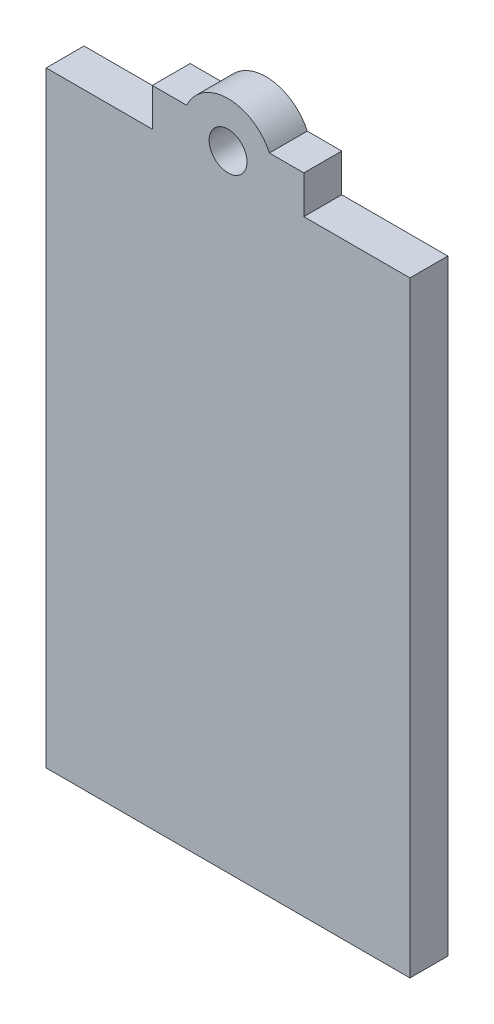
SolidWorks part; units mm, degrees
ref_plane "Front Plane" through (0, 0, 0) normal (0, 0, 1) x (1, 0, 0)
ref_plane "Top Plane" through (0, 0, 0) normal (0, 1, 0) x (1, 0, 0)
ref_plane "Right Plane" through (0, 0, 0) normal (1, 0, 0) x (0, 0, -1)
sketch "Sketch1" plane through (0, 0, 0) normal (0, 0, 1) x (1, 0, 0)
  line L1 (24, 50) -> (-24, 50)
  line L2 (24, 50) -> (24, -50)
  line L3 (24, -50) -> (-24, -50)
  line L4 (-24, 50) -> (-24, -50)
  line L5 (24, 50) -> (-24, -50) construction
  line L6 (24, -50) -> (-24, 50) construction
  point P0 (0, 0)
  dimension "D1" = 48
  dimension "D2" = 100
extrude "Boss-Extrude1" add sketch "Sketch1" along normal blind 5
sketch "Sketch2" plane through (0, 50, 0) normal (0, 1, 0) x (1, 0, 0)
  line L0 (24, -5) -> (-24, -5) construction
  line L1 (-10, -5) -> (10, -5)
  line L2 (-10, -5) -> (-10, 0)
  line L3 (-10, 0) -> (10, 0)
  line L4 (10, -5) -> (10, 0)
  line L5 (24, 0) -> (-24, 0) construction
  line L6 (-24, -5) -> (-24, 0) construction
  line L8 (24, -5) -> (24, 0) construction
  dimension "D1" = 14
  dimension "D2" = 20
  dimension "D3" = 14
  dimension "D4" = 5
extrude "Boss-Extrude2" add sketch "Sketch2" along normal blind 5
mirror "Mirror1" about plane through (0, 0, 0) normal (0, 1, 0) of "Boss-Extrude2"
sketch "Sketch3" plane through (0, 0, 5) normal (0, 0, 1) x (1, 0, 0)
  line L0 (-10, 55) -> (10, 55) construction
  line L1 (-10, 50) -> (-24, 50) construction
  line L2 (10, 55) -> (10, 50) construction
  line L3 (-10, 55) -> (-10, 50) construction
  circle A0 centre (0, 52.5) radius 6
  dimension "D1" = 12
  dimension "D2" = 2.5
  dimension "D3" = 10
  dimension "D4" = 2.5
  dimension "D5" = 10
extrude "Boss-Extrude3" add sketch "Sketch3" against normal blind 5
sketch "Sketch4" plane through (0, 0, 5) normal (0, 0, 1) x (1, 0, 0)
  line L0 (10, 55) -> (10, 50) construction
  line L1 (5.4544, 55) -> (10, 55) construction
  line L2 (-10, 55) -> (-5.4544, 55) construction
  circle A0 centre (0, 52.5) radius 2.5
  arc A2 (5.4544, 55) -> (-5.4544, 55) centre (0, 52.5) ccw construction
  dimension "D1" = 5
  dimension "D2" = 10
  dimension "D3" = 2.5
  dimension "D4" = 3.5
extrude "Cut-Extrude1" cut sketch "Sketch4" against normal blind 5
mirror "Mirror2" about plane through (0, 0, 0) normal (0, 1, 0) of "Boss-Extrude3", "Cut-Extrude1"
sketch "Sketch5" plane through (0, 0, 5) normal (0, 0, 1) x (1, 0, 0)
  line L0 (-24, 50) -> (-24, -50) construction
  line L1 (-24, -30) -> (29.8591, -30)
  line L2 (-24, -30) -> (-24, -58.8208)
  line L3 (-24, -58.8208) -> (29.8591, -58.8208)
  line L4 (29.8591, -30) -> (29.8591, -58.8208)
  line L5 (-24, -50) -> (-10, -50) construction
  dimension "20" = 20
extrude "Cut-Extrude2" cut sketch "Sketch5" against normal blind 10
